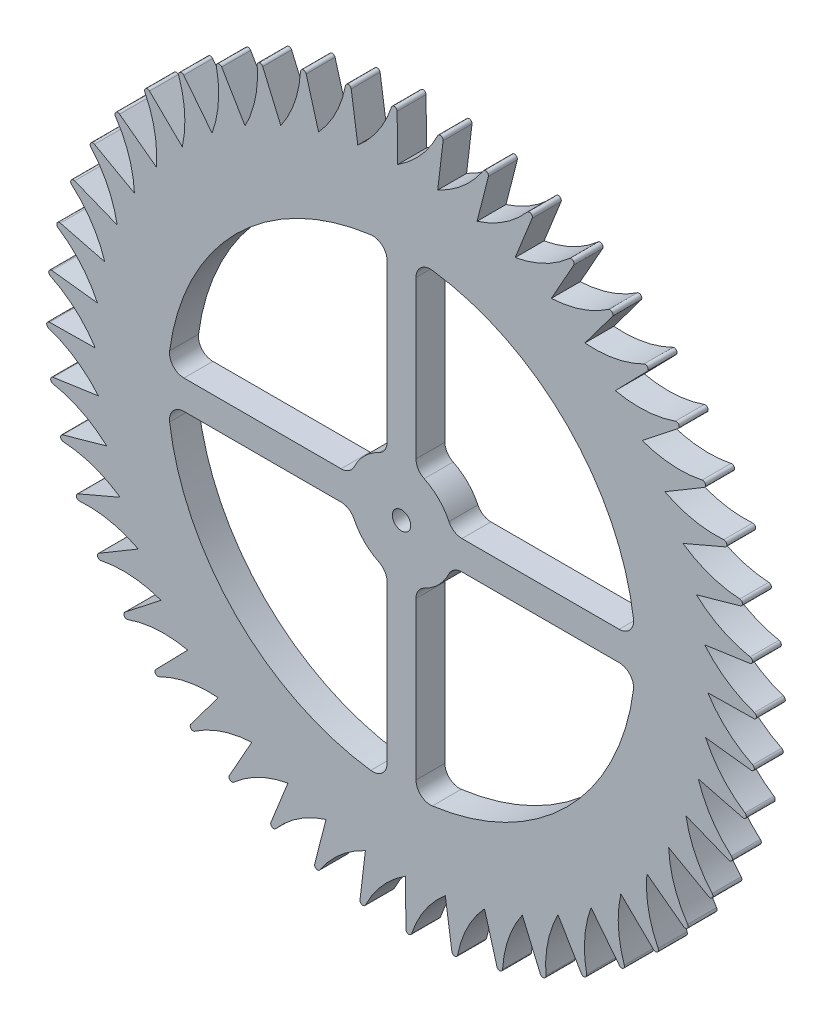
SolidWorks part; units mm, degrees
ref_plane "Front" through (0, 0, 0) normal (0, 0, 1) x (1, 0, 0)
ref_plane "Top" through (0, 0, 0) normal (0, 1, 0) x (1, 0, 0)
ref_plane "Right" through (0, 0, 0) normal (1, 0, 0) x (0, 0, -1)
sketch "Sketch1" plane through (0, 0, 0) normal (0, 0, 1) x (1, 0, 0)
  line L0 (49.2847, 33.4883) -> (49.2648, 35.0757)
  line L1 (48.6197, 86.4432) -> (48.5202, 94.3594)
  line L2 (55.5373, 86.0769) -> (56.472, 93.9384)
  line L3 (62.348, 84.8109) -> (64.3009, 92.4831)
  line L4 (68.9352, 82.6667) -> (71.8728, 90.0184)
  line L5 (75.1862, 79.6811) -> (79.0582, 86.5865)
  line L6 (80.9939, 75.9051) -> (85.7342, 82.246)
  line L7 (86.2592, 71.4033) -> (91.7865, 77.0713)
  line L8 (90.8917, 66.2528) -> (97.1116, 71.1508)
  line L9 (94.8124, 60.5417) -> (101.6184, 64.5859)
  line L10 (97.9541, 54.3677) -> (105.2297, 57.489)
  line L11 (100.263, 47.8365) -> (107.8838, 49.9814)
  line L12 (101.6997, 41.0597) -> (109.5352, 42.1916)
  line L13 (102.2396, 34.1534) -> (110.1558, 34.2528)
  line L14 (101.8733, 27.2357) -> (109.7348, 26.301)
  line L15 (100.6073, 20.425) -> (108.2795, 18.4722)
  line L16 (98.4631, 13.8379) -> (105.8148, 10.9003)
  line L17 (95.4775, 7.5869) -> (102.3829, 3.7149)
  line L18 (91.7015, 1.7791) -> (98.0424, -2.9611)
  line L19 (87.1997, -3.4861) -> (92.8676, -9.0134)
  line L20 (82.0492, -8.1187) -> (86.9472, -14.3385)
  line L21 (76.3381, -12.0393) -> (80.3823, -18.8453)
  line L22 (70.1641, -15.181) -> (73.2854, -22.4566)
  line L23 (63.6329, -17.49) -> (65.7778, -25.1107)
  line L24 (56.8561, -18.9266) -> (57.988, -26.7622)
  line L25 (49.9498, -19.4665) -> (50.0492, -27.3827)
  line L26 (43.0321, -19.1003) -> (42.0974, -26.9617)
  line L27 (36.2214, -17.8342) -> (34.2686, -25.5064)
  line L28 (29.6343, -15.69) -> (26.6967, -23.0417)
  line L29 (23.3833, -12.7044) -> (19.5113, -19.6098)
  line L30 (17.5755, -8.9284) -> (12.8353, -15.2693)
  line L31 (12.3103, -4.4267) -> (6.783, -10.0946)
  line L32 (7.6777, 0.7238) -> (1.4579, -4.1741)
  line L33 (3.7571, 6.435) -> (-3.0489, 2.3907)
  line L34 (0.6154, 12.609) -> (-6.6602, 9.4877)
  line L35 (-1.6936, 19.1402) -> (-9.3143, 16.9953)
  line L36 (-3.1302, 25.917) -> (-10.9658, 24.7851)
  line L37 (-3.6701, 32.8233) -> (-11.5863, 32.7238)
  line L38 (-3.3039, 39.7409) -> (-11.1653, 40.6757)
  line L39 (-2.0378, 46.5516) -> (-9.71, 48.5045)
  line L40 (0.1063, 53.1388) -> (-7.2453, 56.0764)
  line L41 (3.092, 59.3898) -> (-3.8134, 63.2618)
  line L42 (6.868, 65.1976) -> (0.5271, 69.9378)
  line L43 (11.3697, 70.4628) -> (5.7018, 75.9901)
  line L44 (16.5202, 75.0954) -> (11.6223, 81.3152)
  line L45 (22.2313, 79.016) -> (18.1871, 85.822)
  line L46 (28.4053, 82.1577) -> (25.2841, 89.4333)
  line L47 (34.9366, 84.4666) -> (32.7917, 92.0874)
  line L48 (41.7134, 85.9033) -> (40.5815, 93.7388)
  circle A0 centre (49.2847, 33.4883) radius 1.5875
  arc A2 (41.7134, 85.9033) -> (47.5455, 94.51) centre (29.4577, 100.4876) ccw
  arc A4 (48.5202, 94.3594) -> (47.5455, 94.51) centre (48.0203, 94.3531) ccw
  arc A5 (48.6197, 86.4432) -> (55.5253, 94.215) centre (38.3724, 102.5023) ccw
  arc A6 (56.472, 93.9384) -> (55.5253, 94.215) centre (55.9755, 93.9975) ccw
  arc A7 (55.5373, 86.0769) -> (63.3984, 92.8809) centre (47.4739, 103.3363) ccw
  arc A8 (64.3009, 92.4831) -> (63.3984, 92.8809) centre (63.8163, 92.6065) ccw
  arc A9 (62.348, 84.8109) -> (71.0299, 90.5306) centre (56.6064, 102.9751) ccw
  arc A10 (71.8728, 90.0184) -> (71.0299, 90.5306) centre (71.4085, 90.2039) ccw
  arc A11 (68.9352, 82.6667) -> (78.2894, 87.2043) centre (65.6136, 101.4249) ccw
  arc A12 (79.0582, 86.5865) -> (78.2894, 87.2043) centre (78.6221, 86.831) ccw
  arc A13 (75.1862, 79.6811) -> (85.0526, 82.9588) centre (74.3414, 98.7124) ccw
  arc A14 (85.7342, 82.246) -> (85.0526, 82.9588) centre (85.3337, 82.5454) ccw
  arc A15 (80.9939, 75.9051) -> (91.2038, 77.867) centre (82.6405, 94.8838) ccw
  arc A16 (91.7865, 77.0713) -> (91.2038, 77.867) centre (91.4285, 77.4203) ccw
  arc A17 (86.2592, 71.4033) -> (96.6377, 72.0158) centre (90.3688, 90.0048) ccw
  arc A18 (97.1116, 71.1508) -> (96.6377, 72.0158) centre (96.8022, 71.5436) ccw
  arc A19 (90.8917, 66.2528) -> (101.2614, 65.5054) centre (97.3942, 84.1587) ccw
  arc A20 (101.6184, 64.5859) -> (101.2614, 65.5054) centre (101.3629, 65.0158) ccw
  arc A21 (94.8124, 60.5417) -> (104.9958, 58.4471) centre (103.5964, 77.4457) ccw
  arc A22 (105.2297, 57.489) -> (104.9958, 58.4471) centre (105.0326, 57.9485) ccw
  arc A23 (97.9541, 54.3677) -> (107.777, 50.9619) centre (108.8694, 69.9805) ccw
  arc A24 (107.8838, 49.9814) -> (107.777, 50.9619) centre (107.7483, 50.4627) ccw
  arc A25 (100.263, 47.8365) -> (109.5573, 43.1776) centre (113.1228, 61.891) ccw
  arc A26 (109.5352, 42.1916) -> (109.5573, 43.1776) centre (109.4638, 42.6864) ccw
  arc A27 (101.6997, 41.0597) -> (110.3064, 35.2276) centre (116.284, 53.3154) ccw
  arc A28 (110.1558, 34.2528) -> (110.3064, 35.2276) centre (110.1495, 34.7528) ccw
  arc A29 (102.2396, 34.1534) -> (110.0114, 27.2477) centre (118.2987, 44.4007) ccw
  arc A30 (109.7348, 26.301) -> (110.0114, 27.2477) centre (109.7938, 26.7975) ccw
  arc A31 (101.8733, 27.2357) -> (108.6773, 19.3747) centre (119.1326, 35.2992) ccw
  arc A32 (108.2795, 18.4722) -> (108.6773, 19.3747) centre (108.4029, 18.9568) ccw
  arc A33 (100.6073, 20.425) -> (106.327, 11.7432) centre (118.7714, 26.1667) ccw
  arc A34 (105.8148, 10.9003) -> (106.327, 11.7432) centre (106.0003, 11.3646) ccw
  arc A35 (98.4631, 13.8379) -> (103.0006, 4.4837) centre (117.2213, 17.1595) ccw
  arc A36 (102.3829, 3.7149) -> (103.0006, 4.4837) centre (102.6274, 4.151) ccw
  arc A37 (95.4775, 7.5869) -> (98.7552, -2.2795) centre (114.5088, 8.4317) ccw
  arc A38 (98.0424, -2.9611) -> (98.7552, -2.2795) centre (98.3418, -2.5606) ccw
  arc A39 (91.7015, 1.7791) -> (93.6634, -8.4307) centre (110.6802, 0.1326) ccw
  arc A40 (92.8676, -9.0134) -> (93.6634, -8.4307) centre (93.2167, -8.6554) ccw
  arc A41 (87.1997, -3.4861) -> (87.8122, -13.8646) centre (105.8012, -7.5957) ccw
  arc A42 (86.9472, -14.3385) -> (87.8122, -13.8646) centre (87.34, -14.0292) ccw
  arc A43 (82.0492, -8.1187) -> (81.3018, -18.4884) centre (99.9551, -14.6211) ccw
  arc A44 (80.3823, -18.8453) -> (81.3018, -18.4884) centre (80.8122, -18.5899) ccw
  arc A45 (76.3381, -12.0393) -> (74.2435, -22.2228) centre (93.2421, -20.8234) ccw
  arc A46 (73.2854, -22.4566) -> (74.2435, -22.2228) centre (73.7449, -22.2595) ccw
  arc A47 (70.1641, -15.181) -> (66.7582, -25.0039) centre (85.7769, -26.0963) ccw
  arc A48 (65.7778, -25.1107) -> (66.7582, -25.0039) centre (66.2591, -24.9752) ccw
  arc A49 (63.6329, -17.49) -> (58.974, -26.7843) centre (77.6873, -30.3497) ccw
  arc A50 (57.988, -26.7622) -> (58.974, -26.7843) centre (58.4828, -26.6907) ccw
  arc A51 (56.8561, -18.9266) -> (51.0239, -27.5333) centre (69.1118, -33.5109) ccw
  arc A52 (50.0492, -27.3827) -> (51.0239, -27.5333) centre (50.5492, -27.3764) ccw
  arc A53 (49.9498, -19.4665) -> (43.0441, -27.2383) centre (60.197, -35.5256) ccw
  arc A54 (42.0974, -26.9617) -> (43.0441, -27.2383) centre (42.5939, -27.0208) ccw
  arc A55 (43.0321, -19.1003) -> (35.1711, -25.9042) centre (51.0956, -36.3596) ccw
  arc A56 (34.2686, -25.5064) -> (35.1711, -25.9042) centre (34.7531, -25.6298) ccw
  arc A57 (36.2214, -17.8342) -> (27.5396, -23.5539) centre (41.9631, -35.9984) ccw
  arc A58 (26.6967, -23.0417) -> (27.5396, -23.5539) centre (27.161, -23.2273) ccw
  arc A59 (29.6343, -15.69) -> (20.2801, -20.2276) centre (32.9559, -34.4482) ccw
  arc A60 (19.5113, -19.6098) -> (20.2801, -20.2276) centre (19.9474, -19.8543) ccw
  arc A61 (23.3833, -12.7044) -> (13.5169, -15.9822) centre (24.2281, -31.7357) ccw
  arc A62 (12.8353, -15.2693) -> (13.5169, -15.9822) centre (13.2358, -15.5687) ccw
  arc A63 (17.5755, -8.9284) -> (7.3657, -10.8903) centre (15.929, -27.9071) ccw
  arc A64 (6.783, -10.0946) -> (7.3657, -10.8903) centre (7.141, -10.4437) ccw
  arc A65 (12.3103, -4.4267) -> (1.9318, -5.0391) centre (8.2006, -23.0281) ccw
  arc A66 (1.4579, -4.1741) -> (1.9318, -5.0391) centre (1.7672, -4.5669) ccw
  arc A67 (7.6777, 0.7238) -> (-2.692, 1.4713) centre (1.1752, -17.182) ccw
  arc A68 (-3.0489, 2.3907) -> (-2.692, 1.4713) centre (-2.7935, 1.9609) ccw
  arc A69 (3.7571, 6.435) -> (-6.4264, 8.5295) centre (-5.027, -10.469) ccw
  arc A70 (-6.6602, 9.4877) -> (-6.4264, 8.5295) centre (-6.4631, 9.0282) ccw
  arc A71 (0.6154, 12.609) -> (-9.2075, 16.0148) centre (-10.2999, -3.0038) ccw
  arc A72 (-9.3143, 16.9953) -> (-9.2075, 16.0148) centre (-9.1789, 16.514) ccw
  arc A73 (-1.6936, 19.1402) -> (-10.9879, 23.7991) centre (-14.5533, 5.0857) ccw
  arc A74 (-10.9658, 24.7851) -> (-10.9879, 23.7991) centre (-10.8943, 24.2903) ccw
  arc A75 (-3.1302, 25.917) -> (-11.7369, 31.7491) centre (-17.7145, 13.6613) ccw
  arc A76 (-11.5863, 32.7238) -> (-11.7369, 31.7491) centre (-11.58, 32.2239) ccw
  arc A77 (-3.6701, 32.8233) -> (-11.4419, 39.7289) centre (-19.7293, 22.576) ccw
  arc A78 (-11.1653, 40.6757) -> (-11.4419, 39.7289) centre (-11.2244, 40.1791) ccw
  arc A79 (-3.3039, 39.7409) -> (-10.1078, 47.602) centre (-20.5632, 31.6775) ccw
  arc A80 (-9.71, 48.5045) -> (-10.1078, 47.602) centre (-9.8334, 48.0199) ccw
  arc A81 (-2.0378, 46.5516) -> (-7.7575, 55.2335) centre (-20.202, 40.81) ccw
  arc A82 (-7.2453, 56.0764) -> (-7.7575, 55.2335) centre (-7.4309, 55.6121) ccw
  arc A83 (0.1063, 53.1388) -> (-4.4312, 62.493) centre (-18.6518, 49.8172) ccw
  arc A84 (-3.8134, 63.2618) -> (-4.4312, 62.493) centre (-4.0579, 62.8257) ccw
  arc A85 (3.092, 59.3898) -> (-0.1858, 69.2562) centre (-15.9393, 58.545) ccw
  arc A86 (0.5271, 69.9378) -> (-0.1858, 69.2562) centre (0.2277, 69.5373) ccw
  arc A87 (6.868, 65.1976) -> (4.9061, 75.4074) centre (-12.1107, 66.8441) ccw
  arc A88 (5.7018, 75.9901) -> (4.9061, 75.4074) centre (5.3527, 75.6321) ccw
  arc A89 (11.3697, 70.4628) -> (10.7573, 80.8413) centre (-7.2317, 74.5724) ccw
  arc A90 (11.6223, 81.3152) -> (10.7573, 80.8413) centre (11.2294, 81.0059) ccw
  arc A91 (16.5202, 75.0954) -> (17.2677, 85.465) centre (-1.3856, 81.5978) ccw
  arc A92 (18.1871, 85.822) -> (17.2677, 85.465) centre (17.7573, 85.5666) ccw
  arc A93 (22.2313, 79.016) -> (24.3259, 89.1994) centre (5.3274, 87.8001) ccw
  arc A94 (25.2841, 89.4333) -> (24.3259, 89.1994) centre (24.8246, 89.2362) ccw
  arc A95 (28.4053, 82.1577) -> (31.8112, 91.9806) centre (12.7926, 93.073) ccw
  arc A96 (32.7917, 92.0874) -> (31.8112, 91.9806) centre (32.3104, 91.9519) ccw
  arc A97 (34.9366, 84.4666) -> (39.5955, 93.7609) centre (20.8821, 97.3264) ccw
  arc A98 (40.5815, 93.7388) -> (39.5955, 93.7609) centre (40.0866, 93.6674) ccw
  point P244 (49.2847, 33.4883)
  dimension "D1" = 19.05
  dimension "D2" = 0.5
extrude "Boss-Extrude1" add sketch "Sketch1" along normal blind 5 contours L48 A98 A97 L47 A96 A95 L46 A94 A93 L45 A92 A91 L44 A90 A89 L43 A88 A87 L42 A86 A85 L41 A84 A83 L40 A82 A81 L39 A80 A79 L38 A78 A77 L37 A76 A75 L36 A74 A73 L35 A72 A71 L34 A70 A69 L33 A68 A67 L32 A66 A65
sketch "Sketch2" plane through (0, 0, 5) normal (0, 0, 1) x (1, 0, 0)
  line L0 (49.2847, 40.0758) -> (49.2847, 76.4473) construction
  line L1 (55.8722, 33.4883) -> (92.2437, 33.4883) construction
  line L2 (51.7847, 43.9416) -> (51.7847, 71.1166)
  line L3 (59.738, 35.9883) -> (86.913, 35.9883)
  line L6 (58.0216, 35.9883) -> (89.6664, 35.9883) construction
  line L7 (51.7847, 42.2252) -> (51.7847, 73.87) construction
  line L8 (59.738, 30.9883) -> (86.913, 30.9883)
  line L9 (51.7847, 23.0351) -> (51.7847, -4.1399)
  line L10 (55.8722, 33.4883) -> (92.2437, 33.4883) construction
  line L11 (49.2847, 26.9008) -> (49.2847, -9.4707) construction
  line L12 (46.7847, 23.0351) -> (46.7847, -4.1399)
  line L13 (38.8315, 30.9883) -> (11.6565, 30.9883)
  line L14 (49.2847, 26.9008) -> (49.2847, -9.4707) construction
  line L15 (42.6972, 33.4883) -> (6.3257, 33.4883) construction
  line L16 (38.8315, 35.9883) -> (11.6565, 35.9883)
  line L17 (46.7847, 43.9416) -> (46.7847, 71.1166)
  line L18 (42.6972, 33.4883) -> (6.3257, 33.4883) construction
  line L19 (49.2847, 40.0758) -> (49.2847, 76.4473) construction
  line L20 (49.2847, 33.4883) -> (49.2847, 64.5598) [skipped]
  line L21 (49.2847, 33.4883) -> (49.9488, 33.4883) [skipped]
  arc A0 (55.8722, 33.4883) -> (49.2847, 40.0758) centre (49.2847, 33.4883) ccw construction
  arc A1 (92.2437, 33.4883) -> (49.2847, 76.4473) centre (49.2847, 33.4883) ccw construction
  arc A2 (89.3912, 38.8176) -> (54.614, 73.5948) centre (49.2847, 33.4883) ccw
  arc A5 (57.4827, 37.4096) -> (53.206, 41.6863) centre (49.2847, 33.4883) ccw
  arc A6 (89.6664, 35.9883) -> (51.7847, 73.87) centre (49.2847, 33.4883) ccw construction
  arc A7 (89.3912, 38.8176) -> (86.913, 35.9883) centre (86.913, 38.4883) cw
  arc A8 (58.0216, 35.9883) -> (51.7847, 42.2252) centre (49.2847, 33.4883) ccw construction
  arc A9 (59.738, 35.9883) -> (57.4827, 37.4096) centre (59.738, 38.4883) cw
  arc A10 (51.7847, 71.1166) -> (54.614, 73.5948) centre (54.2847, 71.1166) cw
  arc A11 (51.7847, 43.9416) -> (53.206, 41.6863) centre (54.2847, 43.9416) ccw
  arc A12 (54.614, -6.6181) -> (89.3912, 28.159) centre (49.2847, 33.4883) ccw
  arc A13 (53.206, 25.2904) -> (57.4827, 29.5671) centre (49.2847, 33.4883) ccw
  arc A14 (54.614, -6.6181) -> (51.7847, -4.1399) centre (54.2847, -4.1399) cw
  arc A15 (51.7847, 23.0351) -> (53.206, 25.2904) centre (54.2847, 23.0351) cw
  arc A16 (86.913, 30.9883) -> (89.3912, 28.159) centre (86.913, 28.4883) cw
  arc A17 (59.738, 30.9883) -> (57.4827, 29.5671) centre (59.738, 28.4883) ccw
  arc A18 (49.2847, 26.9008) -> (55.8722, 33.4883) centre (49.2847, 33.4883) ccw construction
  arc A19 (49.2847, -9.4707) -> (92.2437, 33.4883) centre (49.2847, 33.4883) ccw construction
  arc A20 (9.1783, 28.159) -> (43.9554, -6.6181) centre (49.2847, 33.4883) ccw
  arc A21 (41.0868, 29.5671) -> (45.3635, 25.2904) centre (49.2847, 33.4883) ccw
  arc A22 (9.1783, 28.159) -> (11.6565, 30.9883) centre (11.6565, 28.4883) cw
  arc A23 (38.8315, 30.9883) -> (41.0868, 29.5671) centre (38.8315, 28.4883) cw
  arc A24 (46.7847, -4.1399) -> (43.9554, -6.6181) centre (44.2847, -4.1399) cw
  arc A25 (46.7847, 23.0351) -> (45.3635, 25.2904) centre (44.2847, 23.0351) ccw
  arc A26 (42.6972, 33.4883) -> (49.2847, 26.9008) centre (49.2847, 33.4883) ccw construction
  arc A27 (6.3257, 33.4883) -> (49.2847, -9.4707) centre (49.2847, 33.4883) ccw construction
  arc A28 (43.9554, 73.5948) -> (9.1783, 38.8176) centre (49.2847, 33.4883) ccw
  arc A29 (45.3635, 41.6863) -> (41.0868, 37.4096) centre (49.2847, 33.4883) ccw
  arc A30 (43.9554, 73.5948) -> (46.7847, 71.1166) centre (44.2847, 71.1166) cw
  arc A31 (46.7847, 43.9416) -> (45.3635, 41.6863) centre (44.2847, 43.9416) cw
  arc A32 (11.6565, 35.9883) -> (9.1783, 38.8176) centre (11.6565, 38.4883) cw
  arc A33 (38.8315, 35.9883) -> (41.0868, 37.4096) centre (38.8315, 38.4883) ccw
  arc A34 (49.2847, 40.0758) -> (42.6972, 33.4883) centre (49.2847, 33.4883) ccw construction
  arc A35 (49.2847, 76.4473) -> (6.3257, 33.4883) centre (49.2847, 33.4883) ccw construction
  point P16 (49.2847, 33.4883)
  point P39 (49.2847, 33.4883)
  point P56 (49.2847, 33.4883)
  point P73 (49.2847, 33.4883)
  point P86 (49.2847, 33.4883)
  dimension "D4" = 2.5
  dimension "D3" = 2.5
extrude "Cut-Extrude1" cut sketch "Sketch2" against normal through all
equation "\"D1@Boss-Extrude1\" = \"Face Wd@Sketch2\""
